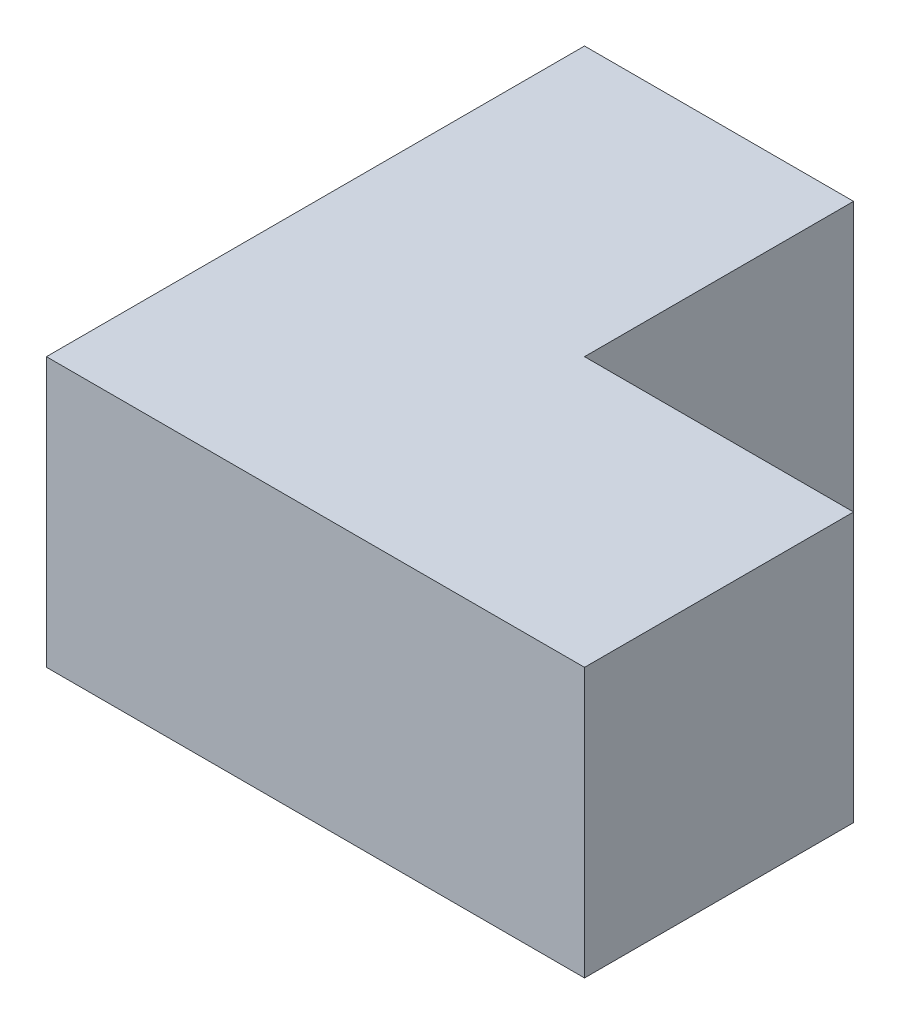
SolidWorks part; units mm, degrees
ref_plane "Front Plane" through (0, 0, 0) normal (0, 0, 1) x (1, 0, 0)
ref_plane "Top Plane" through (0, 0, 0) normal (0, 1, 0) x (1, 0, 0)
ref_plane "Right Plane" through (0, 0, 0) normal (1, 0, 0) x (0, 0, -1)
sketch "Sketch1" plane through (0, 0, 0) normal (0, 1, 0) x (1, 0, 0)
  line L0 (-88.2141, 50.8) -> (-62.8141, 50.8)
  line L1 (-62.8141, 50.8) -> (-62.8141, 25.4)
  line L2 (-62.8141, 25.4) -> (-37.4141, 25.4)
  line L3 (-37.4141, 25.4) -> (-37.4141, 0)
  line L4 (-37.4141, 0) -> (-88.2141, 0)
  line L5 (-88.2141, 0) -> (-88.2141, 50.8)
  dimension "D1" = 50.8
  dimension "D2" = 25.4
  dimension "D3" = 25.4
extrude "Boss-Extrude1" add sketch "Sketch1" along normal blind 25.4
